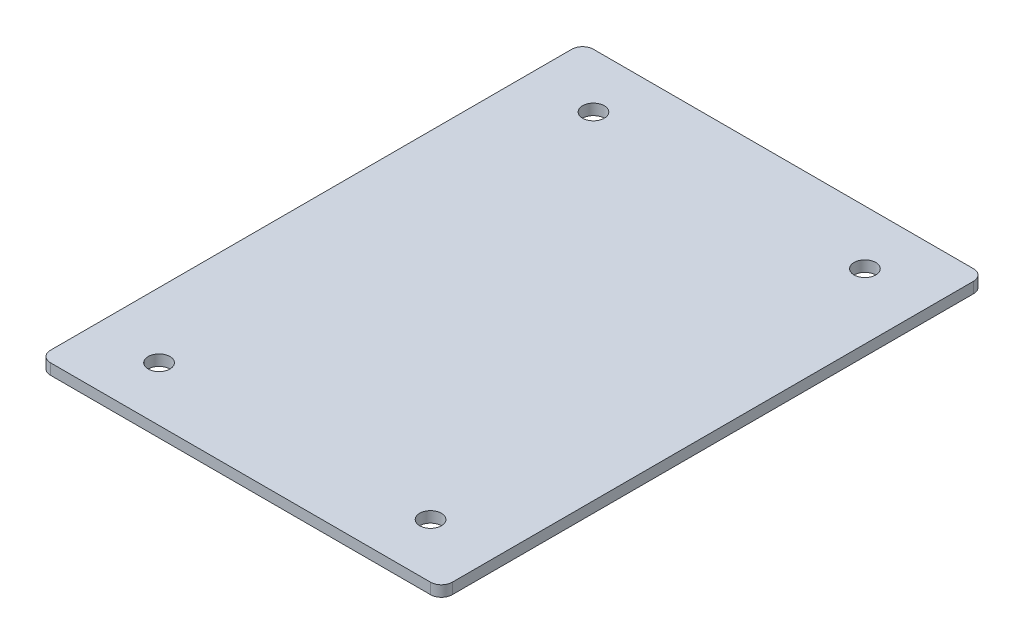
SolidWorks part; units mm, degrees
ref_plane "Front Plane" through (0, 0, 0) normal (0, 0, 1) x (1, 0, 0)
ref_plane "Top Plane" through (0, 0, 0) normal (0, 1, 0) x (1, 0, 0)
ref_plane "Right Plane" through (0, 0, 0) normal (1, 0, 0) x (0, 0, -1)
sketch "Sketch1" plane through (0, 0, 0) normal (0, 1, 0) x (1, 0, 0)
  line L1 (0, 0) -> (74, 0)
  line L2 (0, 0) -> (0, 100)
  line L3 (0, 100) -> (74, 100)
  line L4 (74, 0) -> (74, 100)
  dimension "D1" = 74
  dimension "D2" = 100
extrude "Boss-Extrude1" add sketch "Sketch1" along normal blind 2
fillet "Fillet1" radius 2 4 edges at (0, 1, -100) (74, 1, -100) (0, 1, 0) (74, 1, 0)
sketch "Sketch2" plane through (0, 2, 0) normal (0, 1, 0) x (1, 0, 0)
  line L0 (37, 0) -> (37, 10) construction
  line L1 (12, 90) -> (62, 90) construction
  line L2 (12, 90) -> (12, 10) construction
  line L3 (12, 10) -> (62, 10) construction
  line L4 (62, 90) -> (62, 10) construction
  line L5 (2, 0) -> (72, 0) construction
  line L6 (62, 50) -> (74, 50) construction
  line L7 (74, 2) -> (74, 98) construction
  circle A0 centre (12, 90) radius 2
  circle A1 centre (62, 90) radius 2
  circle A2 centre (62, 10) radius 2
  circle A3 centre (12, 10) radius 2
  dimension "D3" = 4
  dimension "D1" = 80
  dimension "D2" = 50
extrude "Cut-Extrude1" cut sketch "Sketch2" against normal through all
